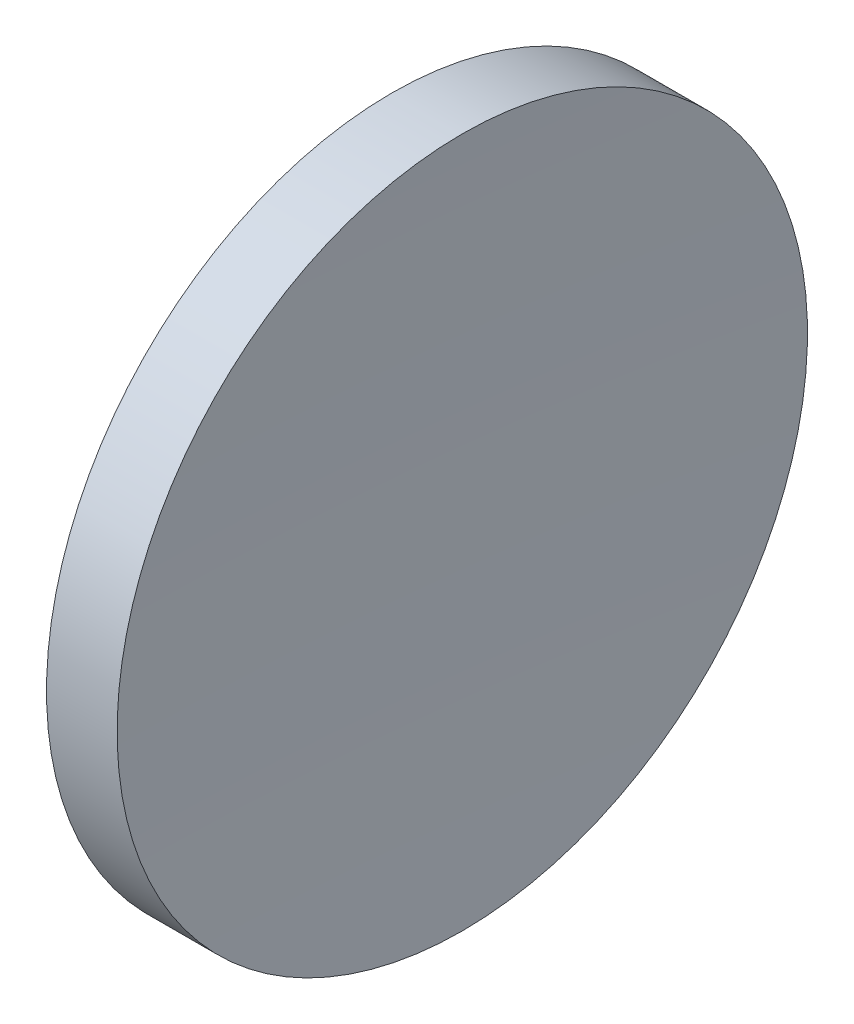
SolidWorks part; units mm, degrees
ref_plane "前视基准面" through (0, 0, 0) normal (0, 0, 1) x (1, 0, 0)
ref_plane "上视基准面" through (0, 0, 0) normal (0, 1, 0) x (1, 0, 0)
ref_plane "右视基准面" through (0, 0, 0) normal (1, 0, 0) x (0, 0, -1)
sketch "草图1" plane through (0, 0, 0) normal (0, 0, 1) x (1, 0, 0)
  line L0 (115.9445, 65.2168) -> (135.9482, 65.2168) construction
  line L1 (123.3119, 77.7168) -> (125.869, 77.7168)
  line L2 (125.6122, 65.2168) -> (122.6122, 65.2168)
  arc A0 (123.3119, 77.7168) -> (122.6122, 65.2168) centre (234.6122, 65.2168) ccw
  arc A1 (125.869, 77.7168) -> (125.6122, 65.2168) centre (430.0122, 65.2168) ccw
revolve "旋转1" add sketch "草图1" angle 360 about L0
